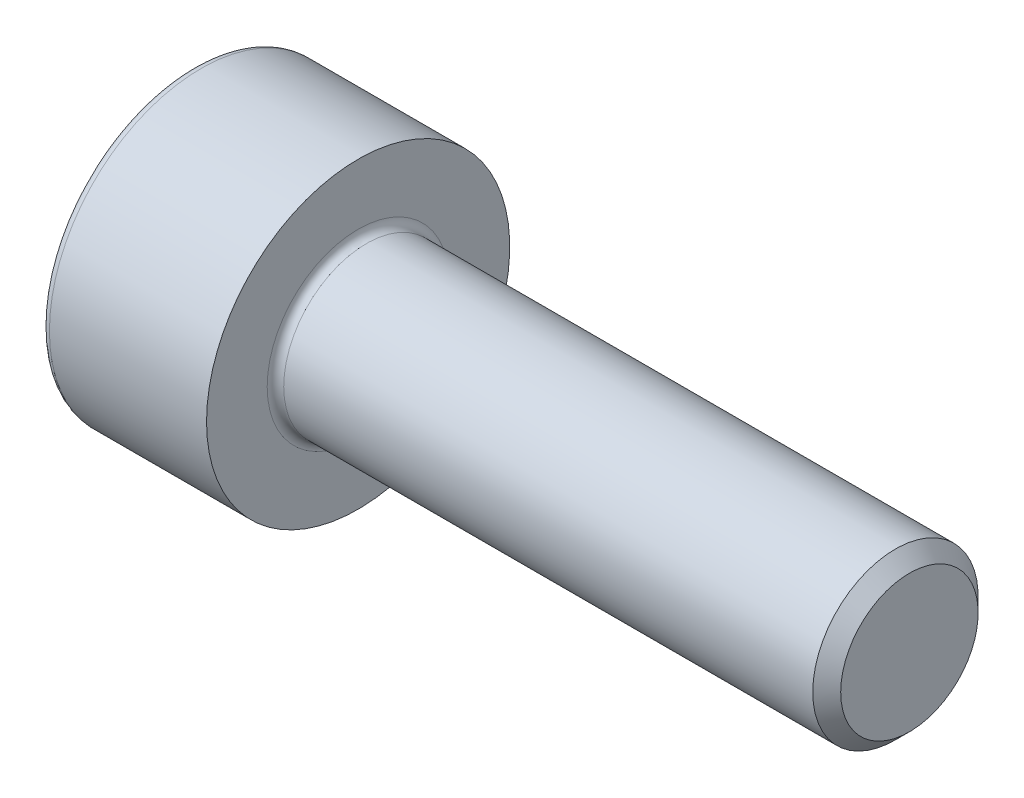
SolidWorks part; units mm, degrees
ref_plane "Front" through (0, 0, 0) normal (0, 0, 1) x (1, 0, 0)
ref_plane "Top" through (0, 0, 0) normal (0, 1, 0) x (1, 0, 0)
ref_plane "Right" through (0, 0, 0) normal (1, 0, 0) x (0, 0, -1)
sketch "Sketch1" plane through (0, 0, 0) normal (0, 0, 1) x (1, 0, 0)
  line L0 (9.7465, 1.5) -> (0.15, 1.5)
  line L1 (-3, 2.6) -> (-3, 0)
  line L2 (0, 2.75) -> (-2.85, 2.75)
  line L3 (0, 1.65) -> (0, 2.75)
  line L4 (10, 1.2465) -> (10, 0)
  line L5 (10, 1.2465) -> (9.7465, 1.5)
  line L6 (-3, 0) -> (0, 0) construction
  line L7 (-3, 0) -> (10, 0)
  arc A0 (-2.85, 2.75) -> (-3, 2.6) centre (-2.85, 2.6) ccw
  arc A1 (0, 1.65) -> (0.15, 1.5) centre (0.15, 1.65) ccw
  point P12 (0, 2.2)
  dimension "D5" = 0.15
  dimension "D1" = 3
  dimension "D2" = 5.5
  dimension "D3" = 135
  dimension "D4" = 0.3585
  dimension "D6" = 10
  dimension "D7" = 3
revolve "Revolve1" add sketch "Sketch1" angle 360 about L7
sketch "Sketch2" plane through (-3, 0, 0) normal (-1, 0, 0) x (0, 0, 1)
  line L7 (1.28, 0.739) -> (0, 1.478)
  line L8 (0, 1.478) -> (-1.28, 0.739)
  line L9 (-1.28, 0.739) -> (-1.28, -0.739)
  line L10 (-1.28, -0.739) -> (0, -1.478)
  line L11 (0, -1.478) -> (1.28, -0.739)
  line L12 (1.28, -0.739) -> (1.28, 0.739)
  circle A0 centre (0, 0) radius 1.28 construction
  dimension "D1" = 2.56
extrude "Cut-Extrude1" cut sketch "Sketch2" against normal blind 1.3
